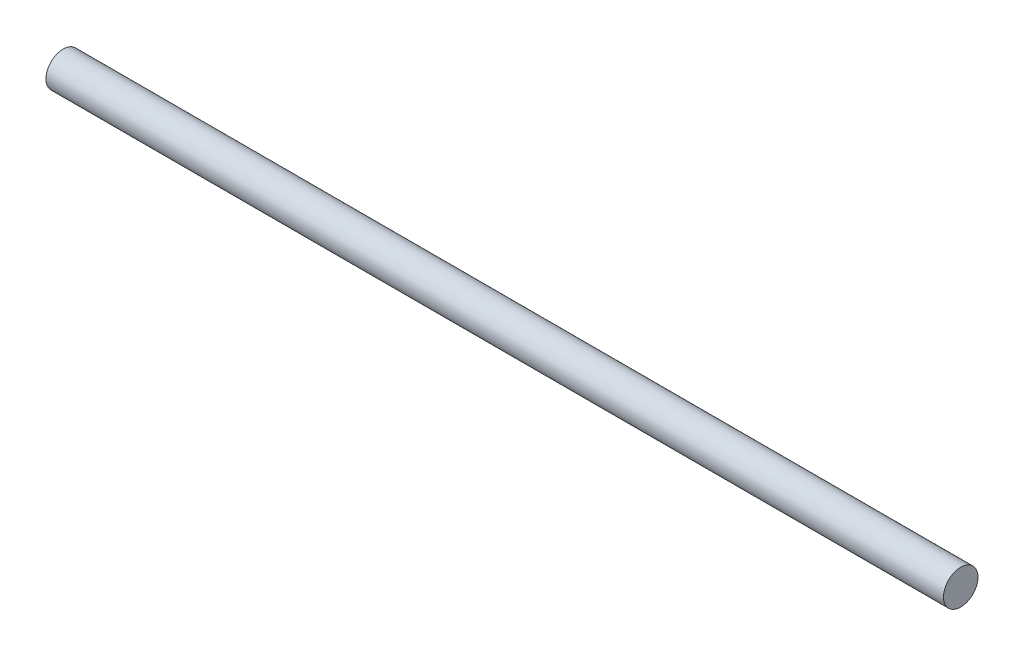
SolidWorks part; units mm, degrees
ref_plane "Front Plane" through (0, 0, 0) normal (0, 0, 1) x (1, 0, 0)
ref_plane "Top Plane" through (0, 0, 0) normal (0, 1, 0) x (1, 0, 0)
ref_plane "Right Plane" through (0, 0, 0) normal (1, 0, 0) x (0, 0, -1)
sketch "Sketch1" plane through (0, 0, 0) normal (1, 0, 0) x (0, 0, -1)
  circle A0 centre (0, 0) radius 6.35
  dimension "D1" = 12.7
extrude "Boss-Extrude1" add sketch "Sketch1" along normal blind 330.2
